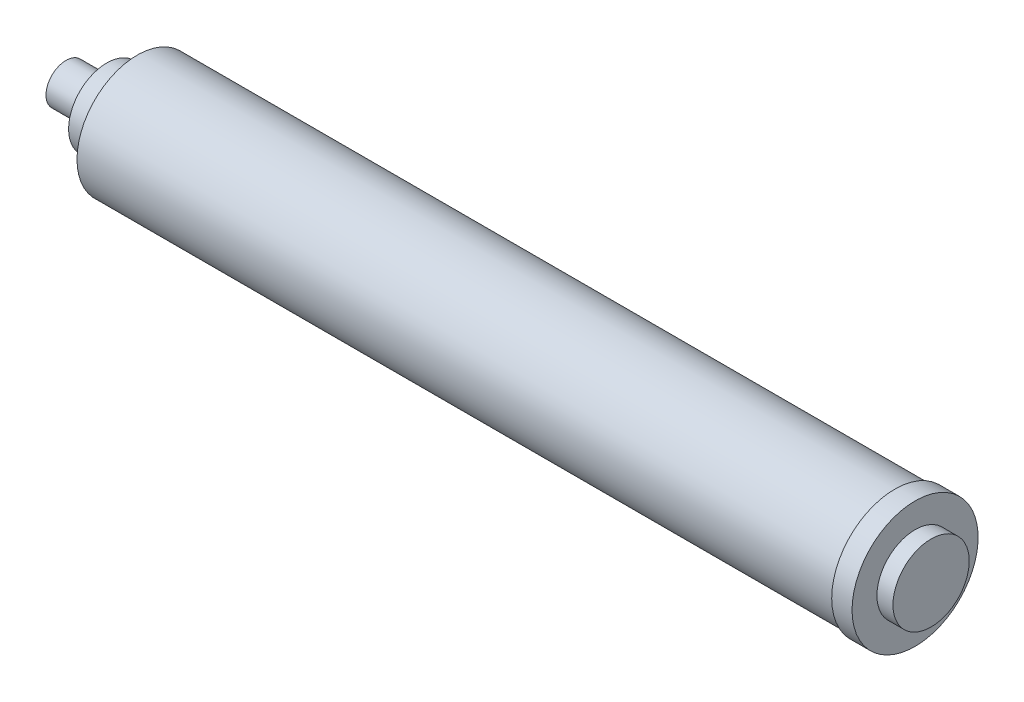
SolidWorks part; units mm, degrees
material "Résine mélamine"
ref_plane "Plan de face" through (0, 0, 0) normal (0, 0, 1) x (1, 0, 0)
ref_plane "Plan de dessus" through (0, 0, 0) normal (0, 1, 0) x (1, 0, 0)
ref_plane "Plan de droite" through (0, 0, 0) normal (1, 0, 0) x (0, 0, -1)
sketch "Esquisse3" plane through (0, 0, 0) normal (0, 0, 1) x (1, 0, 0)
  line L0 (0, 0) -> (0, 39.35)
  line L1 (0, 39.35) -> (-12.7, 39.35)
  line L2 (-12.7, 39.35) -> (-12.7, 37.65)
  line L3 (-12.7, 37.65) -> (-485.5, 37.65)
  line L4 (-485.5, 37.65) -> (-485.5, 0)
  line L5 (-485.5, 0) -> (0, 0)
  line L6 (0, 0) -> (-619.272, 0) construction
  line L7 (-619.272, 0) -> (442.8314, 0) construction
  dimension "D1" = 485.5
  dimension "D2" = 78.7
  dimension "D3" = 12.7
  dimension "D4" = 75.3
revolve "Révolution1" add sketch "Esquisse3" angle 360 about L7
sketch "Esquisse4" plane through (-485.5, 0, 0) normal (-1, 0, 0) x (0, 0, 1)
  circle A0 centre (0, 0) radius 23.8
  dimension "D1" = 47.6
extrude "Boss.-Extru.2" add sketch "Esquisse4" along normal blind 19.1
sketch "Esquisse8" plane through (-504.6, 0, 0) normal (-1, 0, 0) x (0, 0, 1)
  circle A0 centre (0, 0) radius 12.5
  dimension "D1" = 25
extrude "Boss.-Extru.3" add sketch "Esquisse8" along normal blind 25.4
sketch "Esquisse9" plane through (0, 0, 0) normal (1, 0, 0) x (0, 0, -1)
  circle A0 centre (0, 0) radius 23.8
  dimension "D1" = 47.6
extrude "Boss.-Extru.4" add sketch "Esquisse9" along normal blind 10
